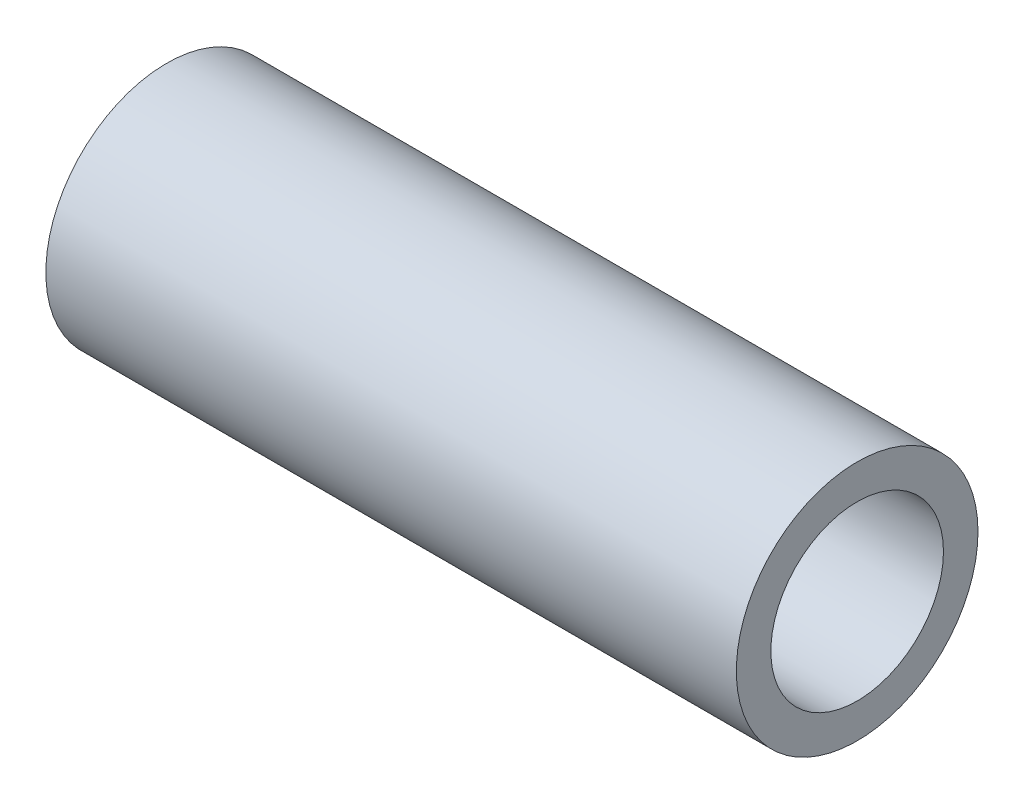
SolidWorks part; units mm, degrees
material "ASTM A36 Steel"
ref_plane "Front Plane" through (0, 0, 0) normal (0, 0, 1) x (1, 0, 0)
ref_plane "Top Plane" through (0, 0, 0) normal (0, 1, 0) x (1, 0, 0)
ref_plane "Right Plane" through (0, 0, 0) normal (1, 0, 0) x (0, 0, -1)
sketch "Sketch1" plane through (0, 0, 0) normal (1, 0, 0) x (0, 0, -1)
  circle A0 centre (0, 0) radius 3.9688
  circle A1 centre (0, 0) radius 5.5563
  dimension "D1" = 7.9375
  dimension "D2" = 1.5875
extrude "Boss-Extrude1" add sketch "Sketch1" along normal mid plane 31.75
